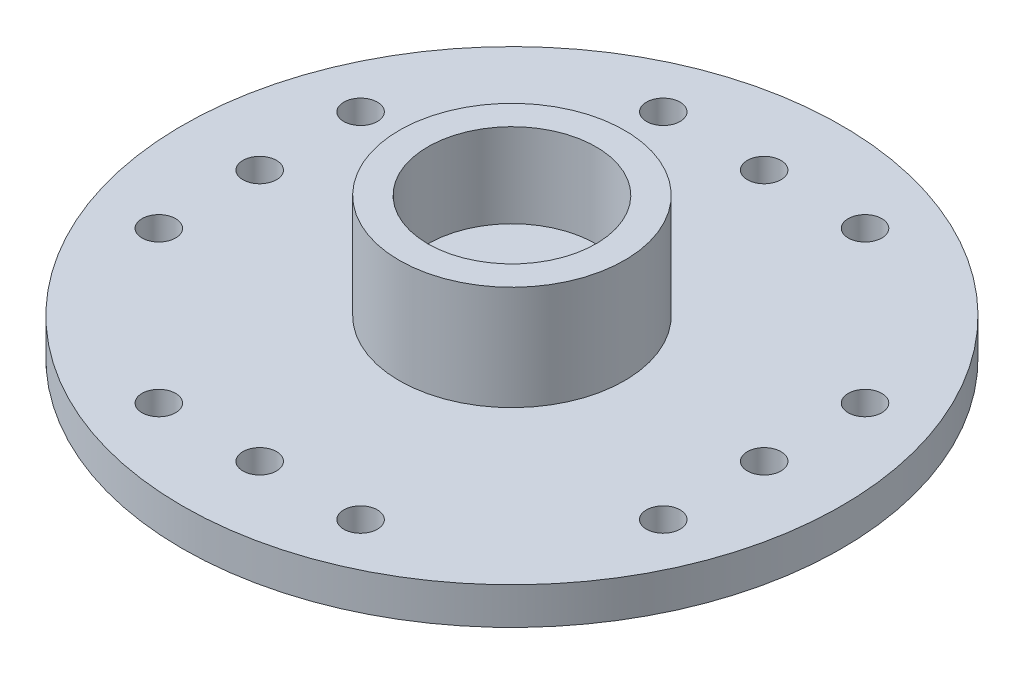
SolidWorks part; units mm, degrees
ref_plane "Front Plane" through (0, 0, 0) normal (0, 0, 1) x (1, 0, 0)
ref_plane "Top Plane" through (0, 0, 0) normal (0, 1, 0) x (1, 0, 0)
ref_plane "Right Plane" through (0, 0, 0) normal (1, 0, 0) x (0, 0, -1)
sketch "Sketch1" plane through (0, 0, 0) normal (0, 1, 0) x (1, 0, 0)
  circle A0 centre (0, 0) radius 9.8
  dimension "D1" = 19.6
extrude "Boss-Extrude1" add sketch "Sketch1" along normal blind 1.1
sketch "Sketch2" plane through (0, 1.1, 0) normal (0, 1, 0) x (1, 0, 0)
  circle A0 centre (0, 0) radius 3.35
  dimension "D1" = 6.7
extrude "Boss-Extrude2" add sketch "Sketch2" along normal blind 3.1
sketch "Sketch3" plane through (0, 4.2, 0) normal (0, 1, 0) x (1, 0, 0)
  circle A0 centre (0, 0) radius 2.5
  dimension "D1" = 5
extrude "Cut-Extrude1" cut sketch "Sketch3" against normal blind 2.5
sketch "Sketch4" plane through (0, 1.7, 0) normal (0, 1, 0) x (1, 0, 0)
  circle A0 centre (0, 0) radius 1
  dimension "D1" = 2
extrude "Cut-Extrude2" cut sketch "Sketch4" against normal up to next
sketch "Sketch5" plane through (0, 0, 0) normal (0, -1, 0) x (1, 0, 0)
  circle A0 centre (0, 0) radius 2
  dimension "D1" = 4
extrude "Cut-Extrude3" cut sketch "Sketch5" against normal blind 0.5
sketch "Sketch6" plane through (0, 0, 0) normal (0, -1, 0) x (1, 0, 0)
  line L0 (-3, 7.5) -> (0, 7.5) construction
  line L1 (0, 7.5) -> (0, 0) construction
  line L2 (0, 7.5) -> (3, 7.5) construction
  circle A0 centre (-3, 7.5) radius 0.5
  circle A1 centre (0, 7.5) radius 0.5
  circle A2 centre (3, 7.5) radius 0.5
  dimension "D1" = 1
  dimension "D2" = 6
  dimension "D3" = 7.5
extrude "Cut-Extrude4" cut sketch "Sketch6" against normal through all
pattern_circular "CirPattern1" count 4 over 360 about axis through (0, 0, 0) along (0, 1, 0) of "Cut-Extrude4"
